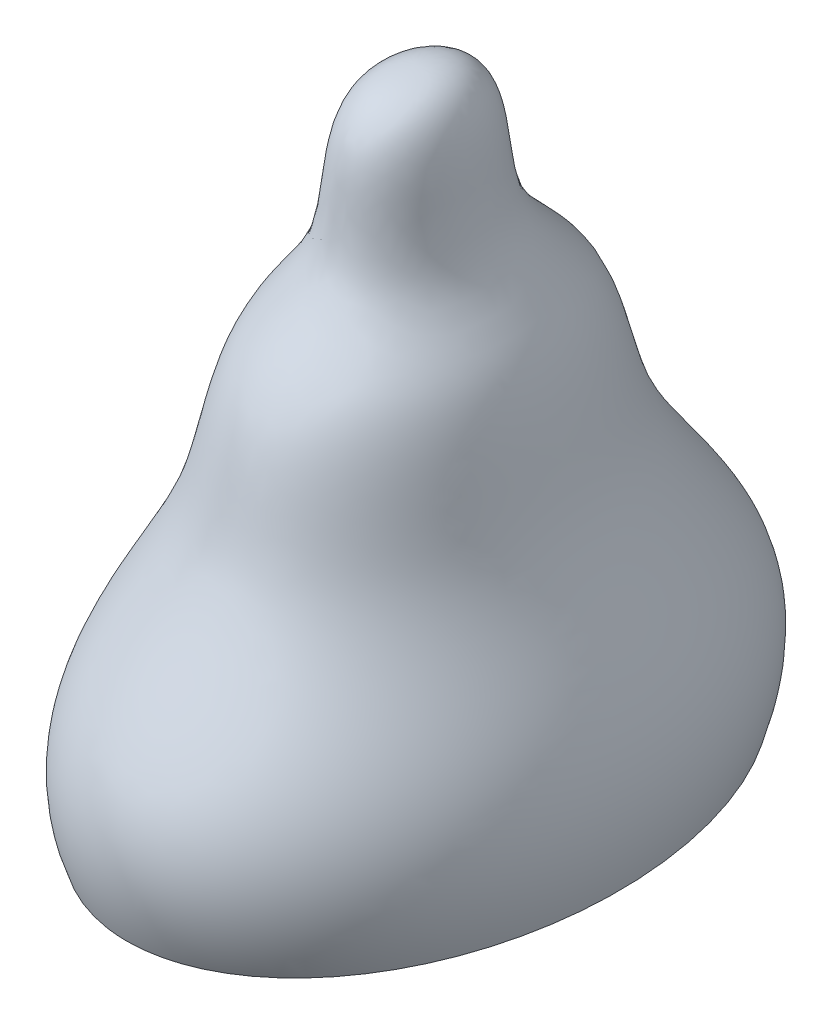
SolidWorks part; units mm, degrees
ref_plane "Ebene vorne" through (0, 0, 0) normal (0, 0, 1) x (1, 0, 0)
ref_plane "Ebene oben" through (0, 0, 0) normal (0, 1, 0) x (1, 0, 0)
ref_plane "Ebene rechts" through (0, 0, 0) normal (1, 0, 0) x (0, 0, -1)
sketch "Skizze1" plane through (0, 0, 0) normal (0, 1, 0) x (1, 0, 0)
  line L0 (0, 100) -> (0, 0) construction
  ellipse E0 centre (0, 0) end of major axis (0, -100) minor radius 70
  dimension "D1" = 200
  dimension "D2" = 140
sketch "Skizze2" plane through (0, 0, 0) normal (1, 0, 0) x (0, 0, -1)
  line L0 (0, 212.4077) -> (0, 0) construction
  line L1 (100, 0) -> (0, 0)
  line L2 (0, 0) -> (0, 212.4077)
  spline S0 degree 3 poles (100, 0) (117.7022, 44.0666) (64.6224, 73.6093) (59.3007, 139.0387) (17.2172, 168.3183) (32.7846, 211.9787) (0, 212.4077) knots 0 0 0 0 0.424256 0.619048 0.743888 1 1 1 1
revolve "Rotation1" add sketch "Skizze2" angle 360 about L0
scale "Skalieren2" scale about origin uniform scaling no x scale factor 0.7 y scale factor 1 z scale factor 1
equation "\"quotient\"=\"D2@Skizze1\"/\"D1@Skizze1\""
